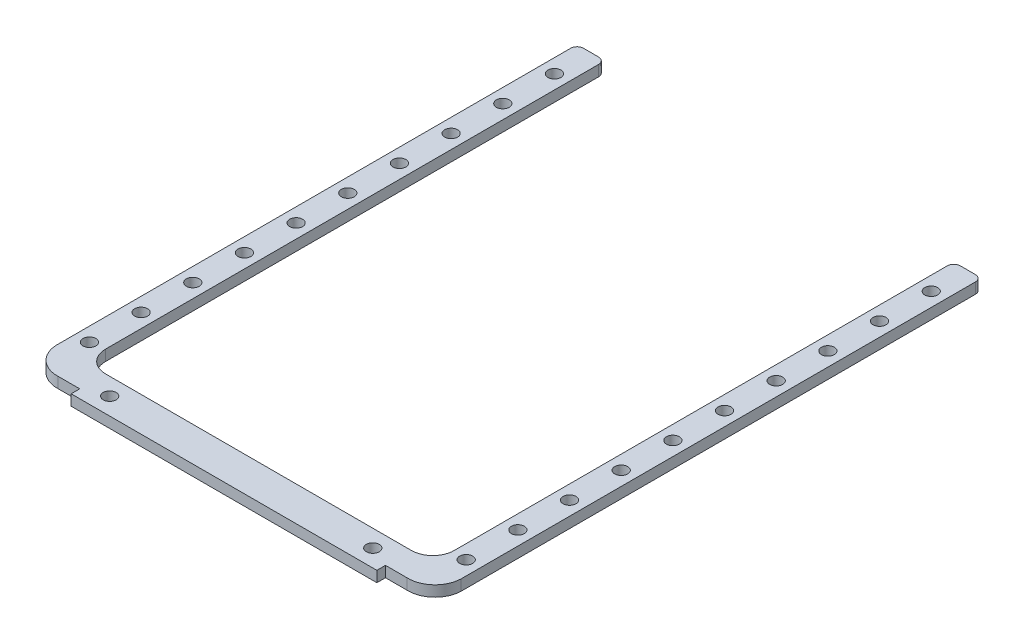
SolidWorks part; units mm, degrees
ref_plane "Front Plane" through (0, 0, 0) normal (0, 0, 1) x (1, 0, 0)
ref_plane "Top Plane" through (0, 0, 0) normal (0, 1, 0) x (1, 0, 0)
ref_plane "Right Plane" through (0, 0, 0) normal (1, 0, 0) x (0, 0, -1)
sketch "Sketch1" plane through (0, 0, 0) normal (0, 1, 0) x (1, 0, 0)
  line L10 (-233.2997, 67.3255) -> (-233.2997, -21.1745)
  line L14 (-139.2997, 67.3255) -> (-139.2997, -21.1745)
  line L26 (-226.7997, 67.3255) -> (-145.7997, 67.3255) construction
  line L28 (-150.7997, -29.1745) -> (-221.7997, -29.1745)
  line L29 (-221.7997, -21.1745) -> (-221.7997, -16.1745) construction
  line L32 (-226.7997, 67.3255) -> (-226.7997, -16.1745)
  line L33 (-145.7997, 67.3255) -> (-145.7997, -16.1745)
  line L34 (-221.7997, -16.1745) -> (-226.7997, -16.1745) construction
  line L35 (-150.7997, -21.1745) -> (-150.7997, -16.1745) construction
  line L36 (-186.2997, 67.3255) -> (-186.2997, -21.1745) construction
  line L37 (-150.7997, -29.1745) -> (-150.7997, -27.1745)
  line L51 (-150.7997, -16.1745) -> (-145.7997, -16.1745) construction
  line L52 (-145.7997, -27.1745) -> (-150.7997, -27.1745)
  line L53 (-150.7997, -21.1745) -> (-221.7997, -21.1745)
  line L58 (-221.7997, -29.1745) -> (-221.7997, -27.1745)
  line L60 (-226.7997, -27.1745) -> (-221.7997, -27.1745)
  line L61 (-233.2997, 67.3255) -> (-233.2997, 99.8255)
  line L62 (-233.2997, 99.8255) -> (-226.7997, 99.8255)
  line L63 (-226.7997, 99.8255) -> (-226.7997, 67.3255)
  line L64 (-145.7997, 67.3255) -> (-145.7997, 99.8255)
  line L65 (-145.7997, 99.8255) -> (-139.2997, 99.8255)
  line L66 (-139.2997, 99.8255) -> (-139.2997, 67.3255)
  arc A8 (-221.7997, -21.1745) -> (-226.7997, -16.1745) centre (-221.7997, -16.1745) cw
  arc A9 (-150.7997, -21.1745) -> (-145.7997, -16.1745) centre (-150.7997, -16.1745) ccw
  arc A10 (-226.7997, -27.1745) -> (-233.2997, -21.1745) centre (-227.0497, -20.9245) cw
  arc A11 (-145.7997, -27.1745) -> (-139.2997, -21.1745) centre (-145.5497, -20.9245) ccw
  point P0 (0, 0)
  point P15 (-150.7997, -27.1745)
  point P23 (-186.2997, -21.1745)
  point P29 (-186.2997, -29.1745)
extrude "Boss-Extrude1" add sketch "Sketch1" along normal blind 2.5
sketch "Sketch2" plane through (0, 2.5, 0) normal (0, 1, 0) x (1, 0, 0)
  line L0 (-186.2997, -29.1745) -> (-186.2997, 110.1569) construction
  line L1 (-221.7997, -29.1745) -> (-150.7997, -29.1745) construction
  line L2 (-230.0497, 55.3255) -> (-230.0497, 67.3255) construction
  line L3 (-142.5497, 55.3255) -> (-142.5497, 67.3255) construction
  line L4 (-230.0497, 67.3255) -> (-230.0497, 79.3255) construction
  line L5 (-142.5497, 67.3255) -> (-142.5497, 79.3255) construction
  line L6 (-230.0497, 55.3255) -> (-230.0497, 43.3255) construction
  line L7 (-142.5497, 55.3255) -> (-142.5497, 43.3255) construction
  line L8 (-230.0497, 43.3255) -> (-230.0497, 31.3255) construction
  line L9 (-142.5497, 43.3255) -> (-142.5497, 31.3255) construction
  line L10 (-230.0497, 31.3255) -> (-230.0497, 19.3255) construction
  line L11 (-142.5497, 31.3255) -> (-142.5497, 19.3255) construction
  line L12 (-230.0497, 19.3255) -> (-230.0497, 7.3255) construction
  line L13 (-142.5497, 19.3255) -> (-142.5497, 7.3255) construction
  line L14 (-230.0497, 7.3255) -> (-230.0497, -4.6745) construction
  line L15 (-142.5497, 7.3255) -> (-142.5497, -4.6745) construction
  line L16 (-230.0497, 79.3255) -> (-230.0497, 91.3255) construction
  line L17 (-142.5497, 79.3255) -> (-142.5497, 91.3255) construction
  line L20 (-230.0497, -4.6745) -> (-230.0497, -16.6745) construction
  line L21 (-142.5497, -4.6745) -> (-142.5497, -16.6745) construction
  circle A0 centre (-230.0497, 7.3255) radius 1.5
  circle A1 centre (-142.5497, 7.3255) radius 1.5
  circle A2 centre (-230.0497, 31.3255) radius 1.5
  circle A3 centre (-230.0497, 55.3255) radius 1.5
  circle A4 centre (-230.0497, 43.3255) radius 1.5
  circle A5 centre (-230.0497, 19.3255) radius 1.5
  circle A6 centre (-230.0497, -4.6745) radius 1.5
  circle A8 centre (-142.5497, -4.6745) radius 1.5
  circle A13 centre (-142.5497, 19.3255) radius 1.5
  circle A14 centre (-142.5497, 31.3255) radius 1.5
  circle A15 centre (-142.5497, 43.3255) radius 1.5
  circle A16 centre (-142.5497, 55.3255) radius 1.5
  circle A17 centre (-230.0497, -16.6745) radius 1.5
  circle A18 centre (-142.5497, -16.6745) radius 1.5
  circle A20 centre (-216.8545, -25.1745) radius 1.5
  circle A21 centre (-155.745, -25.1745) radius 1.5
  circle A22 centre (-230.0497, 67.3255) radius 1.5
  circle A23 centre (-142.5497, 67.3255) radius 1.5
  circle A24 centre (-230.0497, 79.3255) radius 1.5
  circle A25 centre (-142.5497, 79.3255) radius 1.5
  circle A26 centre (-230.0497, 91.3255) radius 1.5
  circle A27 centre (-142.5497, 91.3255) radius 1.5
extrude "Cut-Extrude1" cut sketch "Sketch2" against normal up to surface (2.5 mm away) up to face at (-186.2997, 0, -6.9027)
fillet "Fillet1" radius 1.5 4 edges at (-139.2997, 1.25, -99.8255) (-145.7997, 1.25, -99.8255) (-226.7997, 1.25, -99.8255) (-233.2997, 1.25, -99.8255)
